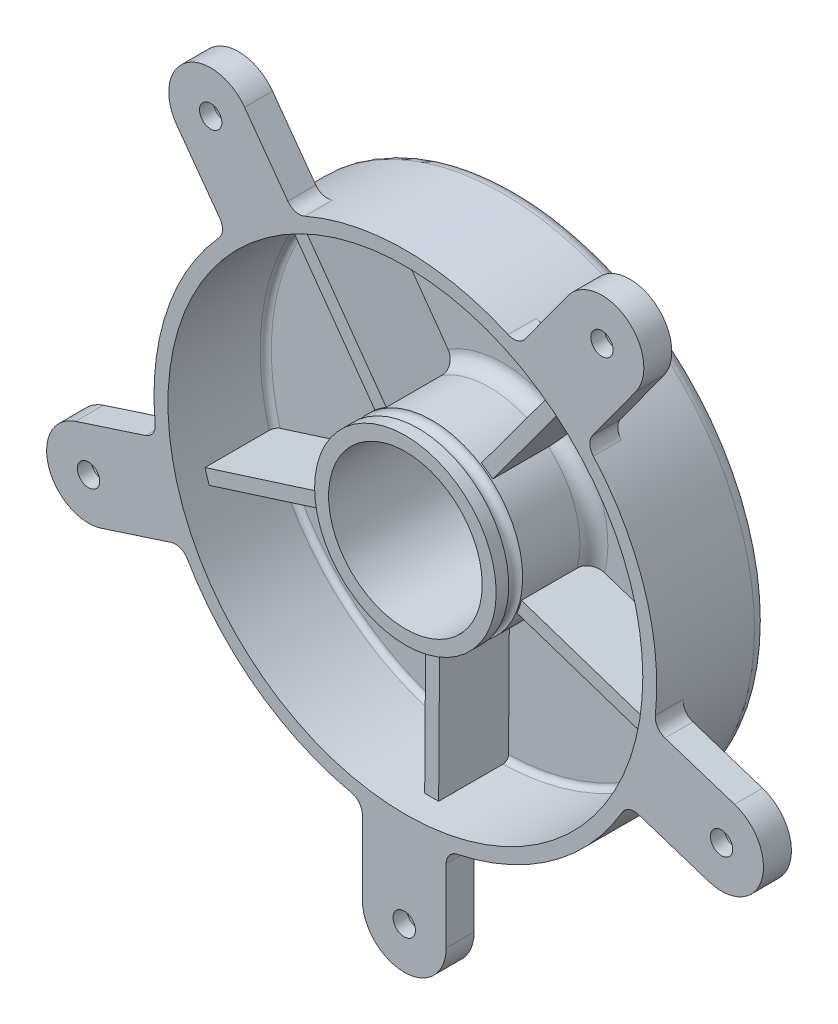
SolidWorks part; units mm, degrees
ref_plane "Ön Düzlem" through (0, 0, 0) normal (0, 0, 1) x (1, 0, 0)
ref_plane "Üst Düzlem" through (0, 0, 0) normal (0, 1, 0) x (1, 0, 0)
ref_plane "Sağ Düzlem" through (0, 0, 0) normal (1, 0, 0) x (0, 0, -1)
sketch "Çizim1" plane through (0, 0, 0) normal (0, 0, 1) x (1, 0, 0)
  circle A0 centre (0, 0) radius 90
  circle A1 centre (0, 0) radius 85
  circle A2 centre (0, 0) radius 32.5
  circle A3 centre (0, 0) radius 27.5
  dimension "D1" = 180
  dimension "D2" = 5
  dimension "D3" = 65
  dimension "D4" = 5
extrude "Yükseklik-Ekstrüzyon1" add sketch "Çizim1" along normal blind 40 contours A0 A1 | A2 A3
sketch "Çizim2" plane through (0, 0, 0) normal (0, 0, 1) x (1, 0, 0)
  circle A0 centre (0, 0) radius 85
extrude "Yükseklik-Ekstrüzyon2" add sketch "Çizim2" along normal blind 5
sketch "Çizim3" plane through (0, 0, 0) normal (0, 0, 1) x (1, 0, 0)
  line L0 (-18.9198, 26.4252) -> (-49.4826, 69.112) construction
  line L1 (19.2853, 26.1596) -> (50.4385, 68.4175) construction
  line L2 (30.8388, -10.2576) -> (80.6553, -26.8277) construction
  line L3 (-0.2259, -32.4992) -> (-0.5908, -84.9979) construction
  line L4 (-30.9784, -9.828) -> (-81.0204, -25.7039) construction
  line L5 (-51.4939, 67.6268) -> (-20.8965, 24.8915)
  line L6 (-47.4285, 70.5375) -> (-16.831, 27.8023)
  line L7 (48.4044, 69.8714) -> (17.2159, 27.5656)
  line L8 (52.429, 66.9044) -> (21.2404, 24.5986)
  line L9 (81.4094, -24.4439) -> (31.5365, -7.855)
  line L10 (79.8313, -29.1883) -> (29.9584, -12.5995)
  line L11 (1.9094, -84.9786) -> (2.2747, -32.4203)
  line L12 (-3.0905, -84.9438) -> (-2.7252, -32.3855)
  line L13 (-80.2294, -28.0758) -> (-30.1306, -12.1818)
  line L14 (-81.7414, -23.3099) -> (-31.6426, -7.4159)
  circle A0 centre (0, 0) radius 32.5
  circle A1 centre (0, 0) radius 85
  point P17 (0, 0)
  point P37 (0, 0)
  dimension "D2" = 170
  dimension "D3" = 65
  dimension "D4" = 2.5
  dimension "D1" = 5
  dimension "D5" = 5
extrude "Yükseklik-Ekstrüzyon3" add sketch "Çizim3" along normal blind 30 contours L6 A1 L5 A0 | L8 A1 L7 A0 | L10 A1 L9 A0 | L12 A1 L11 A0 | L14 A1 L13 A0
ref_plane "Düzlem1" through (0, 0, 40) normal (0, 0, 1) x (1, 0, 0)
sketch "Çizim5" plane through (0, 0, 40) normal (0, 0, 1) x (1, 0, 0)
  line L0 (-0.4078, -84.999) -> (-0.4078, -131.3983) construction
  line L1 (14.5922, -119.1488) -> (14.5922, -92.9578)
  line L2 (-0.4078, -32.4974) -> (-0.4078, -84.999) construction
  line L3 (-15.4078, -119.1488) -> (-15.4078, -92.7821)
  line L4 (-118.0785, -22.1653) -> (-93.0023, -14.0175)
  line L5 (-108.808, -50.697) -> (-83.8989, -42.6035)
  line L6 (-3.0905, -84.9438) -> (-2.7252, -32.3855) construction
  line L7 (-57.5687, 105.4499) -> (-42.0708, 84.1188)
  line L8 (-81.8393, 87.8164) -> (-66.4445, 66.6273)
  line L9 (82.4991, 87.3369) -> (67.0011, 66.0058)
  line L10 (58.2286, 104.9705) -> (42.8339, 83.7815)
  line L11 (108.556, -51.4727) -> (83.4798, -43.325)
  line L12 (117.8265, -22.941) -> (92.9173, -14.8475)
  circle A0 centre (0, 0) radius 90
  arc A1 (18.561, -88.0653) -> (14.5922, -92.9578) centre (19.5922, -92.9578) ccw
  arc A2 (-15.4078, -92.7821) -> (-19.3337, -87.8988) centre (-20.4078, -92.7821) ccw
  arc A3 (-15.4078, -119.1488) -> (14.5922, -119.1488) centre (-0.4078, -119.1488) ccw
  circle A4 centre (-0.4078, -119.1488) radius 4
  arc A5 (-93.0023, -14.0175) -> (-89.5712, -8.7748) centre (-94.5474, -9.2623) ccw
  circle A6 centre (0, 0) radius 32.5 construction
  circle A7 centre (0, 0) radius 85 construction
  arc A8 (-118.0785, -22.1653) -> (-108.808, -50.697) centre (-113.4433, -36.4312) ccw
  circle A9 centre (-113.4433, -36.4312) radius 4
  arc A10 (-78.0194, -44.8662) -> (-83.8989, -42.6035) centre (-82.3538, -47.3588) ccw
  arc A11 (-42.0708, 84.1188) -> (-36.0243, 82.4757) centre (-38.0257, 87.0577) ccw
  arc A12 (-57.5687, 105.4499) -> (-81.8393, 87.8164) centre (-69.704, 96.6331) ccw
  circle A13 centre (-69.704, 96.6331) radius 4
  arc A14 (-66.7796, 60.3364) -> (-66.4445, 66.6273) centre (-70.4896, 63.6884) ccw
  arc A15 (67.0011, 66.0058) -> (67.307, 59.7476) centre (71.0462, 63.0669) ccw
  arc A16 (82.4991, 87.3369) -> (58.2286, 104.9705) centre (70.3639, 96.1537) ccw
  circle A17 centre (70.3639, 96.1537) radius 4
  arc A18 (36.7473, 82.1562) -> (42.8339, 83.7815) centre (38.7888, 86.7204) ccw
  arc A19 (83.4798, -43.325) -> (77.6223, -45.5497) centre (81.9347, -48.0802) ccw
  arc A20 (108.556, -51.4727) -> (117.8265, -22.941) centre (113.1912, -37.2069) ccw
  circle A21 centre (113.1912, -37.2069) radius 4
  arc A22 (89.4907, -9.5611) -> (92.9173, -14.8475) centre (94.4624, -10.0923) ccw
  point P7 (-0.4078, -58.7482)
  point P25 (-2.9078, -58.6647)
  point P67 (0, 0)
  dimension "D1" = 10
  dimension "D2" = 30
  dimension "D3" = 8
  dimension "D5" = 180
  dimension "D4" = 2.5
  dimension "D6" = 5
extrude "Yükseklik-Ekstrüzyon4" add sketch "Çizim5" against normal blind 10 contours A22 A0 A19 L11 A20 L12 A21 | A18 A0 A15 L9 A16 L10 A17 | A14 A0 A11 L7 A12 L8 A13 | A10 A0 A5 L4 A8 L5 A9 | L3 A3 L1 A1 A0 A2 A4
sketch "Çizim6" plane through (0, 0, 30) normal (0, 0, -1) x (-1, 0, 0)
  circle A0 centre (0.4078, -119.1488) radius 7.5
  circle A1 centre (0, 0) radius 90
  circle A2 centre (0.0007, 0.001) radius 90
  circle A3 centre (-113.1906, -37.2059) radius 7.5
  circle A4 centre (0.0018, 0.0006) radius 90
  circle A5 centre (-70.362, 96.1543) radius 7.5
  circle A6 centre (0.0018, -0.0006) radius 90
  circle A7 centre (69.7058, 96.6325) radius 7.5
  circle A8 centre (0.0007, -0.001) radius 90
  circle A9 centre (113.444, -36.4321) radius 7.5
  point P26 (0.001, 0)
  dimension "D1" = 15
  dimension "D2" = 5
extrude "Kes-Ekstrüzyon2" cut sketch "Çizim6" against normal blind 5 contours A5 | A9 | A3 | A7 | A0
fillet "Radyus6" radius 2 5 edges at (49.4826, -69.112, 5) (81.0204, 25.7039, 5) (-50.4385, -68.4175, 5) (-80.6553, 26.8277, 5) (0.5908, 84.9979, 5)
fillet "Radyus7" radius 5 5 edges at (-30.8388, 10.2576, 5) (0.2259, 32.4992, 5) (30.9784, 9.828, 5) (18.9198, -26.4252, 5) (-19.2853, -26.1596, 5)
fillet "Radyus8" radius 5 1 edges at (90, 0, 0)
sketch "Çizim7" plane through (0, 0, 5) normal (0, 0, 1) x (1, 0, 0)
  circle A0 centre (0, 0) radius 27.5
extrude "Kes-Ekstrüzyon3" cut sketch "Çizim7" against normal blind 45
sketch "Çizim8" plane through (0, 0, 0) normal (0, 1, 0) x (1, 0, 0)
  line L0 (-32.5, -10) -> (-32.5, -40) construction
  line L1 (-78.0194, -40) -> (-19.3337, -40) construction
  circle A0 centre (-32.5, -33) radius 2.49
  dimension "D2" = 4.98
  dimension "D1" = 7
sketch "Çizim11" plane through (0, 0, 0) normal (1, 0, 0) x (0, 0, -1)
  line L0 (0, 0) -> (-46.6722, 0) construction
revolve "Kes-Döndür1" cut sketch "Çizim8" angle 360 about L0
